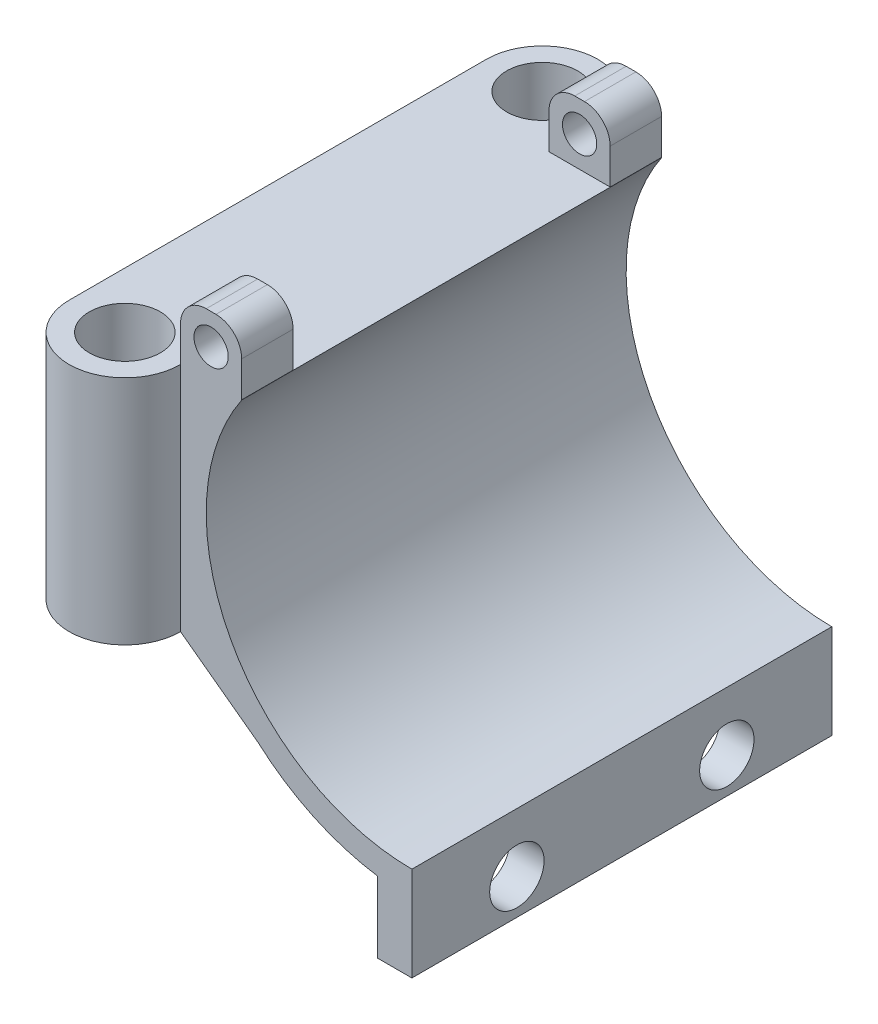
SolidWorks part; units mm, degrees
ref_plane "Front Plane" through (0, 0, 0) normal (0, 0, 1) x (1, 0, 0)
ref_plane "Top Plane" through (0, 0, 0) normal (0, 1, 0) x (1, 0, 0)
ref_plane "Right Plane" through (0, 0, 0) normal (1, 0, 0) x (0, 0, -1)
sketch "Sketch1" plane through (0, 0, 0) normal (0, 1, 0) x (1, 0, 0)
  line L0 (-6.5, 48.7) -> (-6.5, 0)
  line L1 (6.5, 48.7) -> (6.5, 0)
  circle A0 centre (0, 0) radius 4.15
  circle A1 centre (0, 48.7) radius 4.15
  arc A2 (6.5, 48.7) -> (-6.5, 48.7) centre (0, 48.7) ccw
  arc A3 (-6.5, 0) -> (6.5, 0) centre (0, 0) ccw
  point P5 (0, 52.85)
  point P6 (0, -4.15)
  dimension "D1" = 8.3
  dimension "D2" = 8.3
  dimension "D4" = 13
  dimension "D5" = 13
  dimension "D3" = 57
extrude "Boss-Extrude1" add sketch "Sketch1" along normal blind 27
sketch "Sketch2" plane through (0, 0, 0) normal (0, 0, 1) x (1, 0, 0)
  line L0 (6.5, 27) -> (6.5, 0) construction
  line L1 (6.5, 27) -> (6.5, 0)
  line L3 (6.5, 0) -> (15.5686, -6.6857)
  line L4 (6.5, 13.5) -> (60.5, 13.5) construction
  line L5 (57.5, 13.5) -> (62.6383, 13.5)
  line L6 (62.6383, 13.5) -> (62.6383, 10.7828)
  line L7 (62.6383, 10.7828) -> (60.4351, 11.6288)
  line L9 (6.5, 27) -> (13.6569, 27)
  arc A0 (13.6569, 27) -> (57.5, 13.5) centre (33.5, 13.5) ccw
  arc A1 (15.5686, -6.6857) -> (60.4351, 11.6288) centre (33.5, 13.5) ccw
  point P2 (6.5, 13.5)
  dimension "D1" = 48
  dimension "D2" = 54
extrude "Boss-Extrude2" add sketch "Sketch2" against normal blind 49
sketch "Sketch3" plane through (0, 0, 0) normal (0, 0, 1) x (1, 0, 0)
  line L1 (6.5, 27) -> (13.6372, 27)
  line L2 (6.5, 27) -> (6.5, 34.1393)
  line L3 (6.5, 34.1393) -> (13.6372, 34.1393)
  line L4 (13.6372, 27) -> (13.6372, 34.1393)
extrude "Boss-Extrude3" add sketch "Sketch3" against normal up to surface (49 mm away) up to face at (35.2498, 6.6337, -49)
sketch "Sketch4" plane through (0, 0, 0) normal (0, 0, 1) x (1, 0, 0)
  line L0 (13.6372, 34.1393) -> (6.5, 34.1393) construction
  line L1 (6.5, 34.1393) -> (6.5, 27) construction
  circle A0 centre (10.0686, 30.5696) radius 2
  point P0 (10.0686, 34.1393)
  point P1 (6.5, 30.5696)
  dimension "D1" = 4
extrude "Cut-Extrude1" cut sketch "Sketch4" against normal blind 51
fillet "Fillet1" radius 3 2 edges at (13.6372, 34.1393, -24.5) (6.5, 34.1393, -24.5)
sketch "Sketch5" plane through (0, 34.1393, 0) normal (0, 1, 0) x (1, 0, 0)
  line L0 (6.5, 48.7) -> (6.5, 0) construction
  line L1 (6.5, 43) -> (13.6569, 43)
  line L2 (6.5, 43) -> (6.5, 6)
  line L3 (6.5, 6) -> (13.6569, 6)
  line L4 (13.6569, 43) -> (13.6569, 6)
  line L5 (13.6569, 49) -> (13.6569, 0) construction
  line L6 (13.6372, 49) -> (10.6372, 49) construction
  line L7 (10.6372, 0) -> (13.6372, 0) construction
  dimension "D1" = 6
  dimension "D2" = 6
extrude "Cut-Extrude2" cut sketch "Sketch5" against normal up to surface (7.1393 mm away) up to face at (13.647, 27, -24.5)
sketch "Sketch7" plane through (0, 0, 0) normal (0, 0, 1) x (1, 0, 0)
  line L1 (33.5, -20.3769) -> (70.075, -20.3769)
  line L2 (33.5, -20.3769) -> (33.5, 28.1559)
  line L3 (33.5, 28.1559) -> (70.075, 28.1559)
  line L4 (70.075, -20.3769) -> (70.075, 28.1559)
  arc A0 (13.6569, 27) -> (57.5, 13.5) centre (33.5, 13.5) ccw construction
  point P0 (33.5, -10.5)
extrude "Cut-Extrude3" cut sketch "Sketch7" against normal blind 51
sketch "Sketch8" plane through (0, 0, 0) normal (0, 0, 1) x (1, 0, 0)
  line L1 (33.5, -10.5) -> (29.5, -10.5)
  line L2 (33.5, -10.5) -> (33.5, -21.5)
  line L3 (33.5, -21.5) -> (29.5, -21.5)
  line L4 (29.5, -10.5) -> (29.5, -21.5)
  point P5 (33.5, -13.5)
  dimension "D1" = 4
  dimension "D2" = 8
extrude "Boss-Extrude4" add sketch "Sketch8" against normal up to surface (49 mm away) up to face at (12.0686, 30.5696, -49)
sketch "Sketch9" plane through (0, 0, 0) normal (0, 0, 1) x (1, 0, 0)
  line L0 (33.5, 13.5) -> (13.6372, 27)
  line L1 (33.5, 13.5) -> (33.5, -10.5)
  arc A0 (13.6569, 27) -> (33.5, -10.5) centre (33.5, 13.5) ccw construction
  circle A1 centre (33.5, 13.5) radius 24
  point P0 (9.5, 13.5)
  point P1 (33.5, 13.5)
  dimension "D1" = 235.797
sketch "Sketch10" plane through (29.5, 0, 0) normal (-1, 0, 0) x (0, 0, 1)
  line L0 (-49, -21.5) -> (-49, -13.2021) construction
  line L1 (0, -13.2021) -> (0, -21.5) construction
  line L2 (-49, -21.5) -> (0, -21.5) construction
  circle A0 centre (-36.75, -17.351) radius 3.175
  circle A1 centre (-12.25, -17.351) radius 3.175
  point P0 (-49, -17.351)
  point P1 (0, -17.351)
  point P4 (-24.5, -21.5)
  point P7 (-36.75, -21.5)
  point P10 (-12.25, -21.5)
  dimension "D3" = 6.35
  dimension "D4" = 6.35
  dimension "D1" = 12.25
  dimension "D2" = 12.25
extrude "Cut-Extrude4" cut sketch "Sketch10" against normal blind 49
